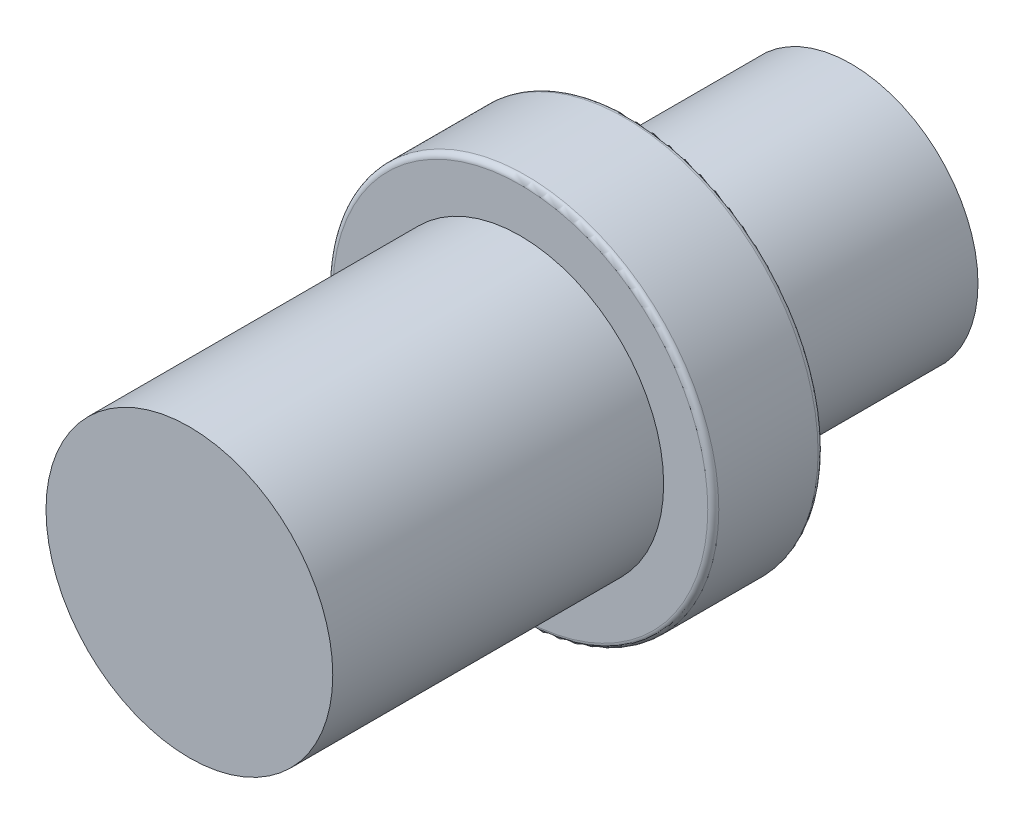
SolidWorks part; units mm, degrees
ref_plane "Front Plane" through (0, 0, 0) normal (0, 0, 1) x (1, 0, 0)
ref_plane "Top Plane" through (0, 0, 0) normal (0, 1, 0) x (1, 0, 0)
ref_plane "Right Plane" through (0, 0, 0) normal (1, 0, 0) x (0, 0, -1)
sketch "Sketch1" plane through (0, 0, 0) normal (0, 0, 1) x (1, 0, 0)
  circle A0 centre (0, 0) radius 11.5
  dimension "D1" = 23
extrude "Boss-Extrude1" add sketch "Sketch1" along normal blind 20
sketch "Sketch2" plane through (0, 0, 20) normal (0, 0, 1) x (1, 0, 0)
  circle A0 centre (0, 0) radius 17.5
  dimension "D1" = 35
extrude "Boss-Extrude2" add sketch "Sketch2" along normal blind 10
sketch "Sketch3" plane through (0, 0, 30) normal (0, 0, 1) x (1, 0, 0)
  circle A0 centre (0, 0) radius 13
  dimension "D1" = 26
extrude "Boss-Extrude3" add sketch "Sketch3" along normal blind 30
fillet "Fillet1" radius 0.5 2 edges at (17.5, 0, 20) (17.5, 0, 30)
